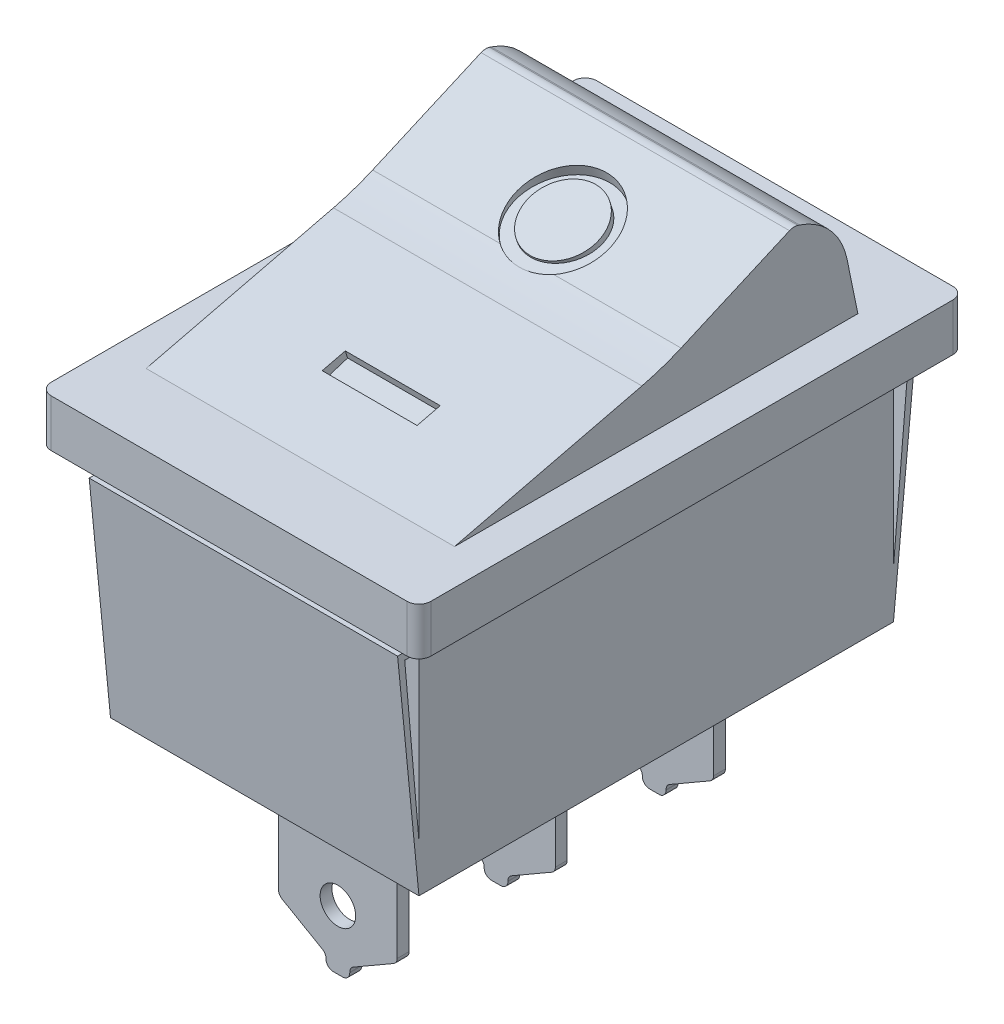
SolidWorks part; units mm, degrees
ref_plane "Alzado" through (0, 0, 0) normal (0, 0, 1) x (1, 0, 0)
ref_plane "Planta" through (0, 0, 0) normal (0, 1, 0) x (1, 0, 0)
ref_plane "Vista lateral" through (0, 0, 0) normal (1, 0, 0) x (0, 0, -1)
sketch "Croquis1" plane through (0, 0, 0) normal (0, 1, 0) x (1, 0, 0)
  line L1 (8, 11.5) -> (-8, 11.5)
  line L2 (8, 11.5) -> (8, -11.5)
  line L3 (8, -11.5) -> (-8, -11.5)
  line L4 (-8, 11.5) -> (-8, -11.5)
  line L5 (8, 11.5) -> (-8, -11.5) construction
  line L6 (8, -11.5) -> (-8, 11.5) construction
  point P0 (0, 0)
  dimension "D1" = 23
  dimension "D2" = 16
extrude "Saliente-Extruir1" add sketch "Croquis1" along normal blind 2
sketch "Croquis2" plane through (0, 0, 0) normal (0, -1, 0) x (1, 0, 0)
  line L1 (6.5, 10) -> (-6.5, 10)
  line L2 (6.5, 10) -> (6.5, -10)
  line L3 (6.5, -10) -> (-6.5, -10)
  line L4 (-6.5, 10) -> (-6.5, -10)
  line L5 (6.5, 10) -> (-6.5, -10) construction
  line L6 (6.5, -10) -> (-6.5, 10) construction
  point P0 (0, 0)
  dimension "D1" = 13
  dimension "D2" = 20
extrude "Saliente-Extruir2" add sketch "Croquis2" along normal blind 10
sketch "Croquis3" plane through (0, 0, 0) normal (1, 0, 0) x (0, 0, -1)
  line L1 (-11.5, 2) -> (11.5, 2) construction
  line L3 (8.5, 2) -> (-8.5, 2)
  line L4 (5.9762, 6.4869) -> (6.0484, 6.463)
  line L5 (8.0421, 4.2212) -> (8.5, 2)
  line L6 (5.7941, 6.5473) -> (8.5, 2) construction
  line L7 (-8.5, 2) -> (-0.6036, 3.9144)
  line L8 (1.0482, 4.4711) -> (5.6184, 6.4704)
  line L9 (-8.5, 2) -> (5.7941, 6.5473) construction
  arc A0 (-0.6036, 3.9144) -> (1.0482, 4.4711) centre (-2.9597, 13.6328) ccw
  arc A1 (8.0421, 4.2212) -> (6.0484, 6.463) centre (5.1039, 3.6155) ccw
  arc A2 (5.9762, 6.4869) -> (5.6184, 6.4704) centre (5.8188, 6.0124) ccw
  point P4 (0.2988, 4.1882)
  point P12 (0.2466, 4.1205)
  point P15 (7.6924, 5.9176)
  dimension "D9" = 10
  dimension "D10" = 3
  dimension "D11" = 0.5
  dimension "D1" = 3
  dimension "D2" = 3
  dimension "D3" = 15
  dimension "D4" = 120
  dimension "D5" = 2
  dimension "D6" = 4
  dimension "D7" = 170
  dimension "D8" = 9
extrude "Saliente-Extruir3" add sketch "Croquis3" along normal mid plane 13
ref_plane "Plano1" through (0, 4.265, 1.3514) normal (0, 0.9533, 0.302) x (1, 0, 0)
sketch "Croquis4" plane through (0, 4.265, 1.3514) normal (0, 0.9533, 0.302) x (1, 0, 0)
  line L0 (0, 4) -> (0, 0) construction
  line L1 (-2, -4.5) -> (-2, -3.5)
  line L2 (-2, -3.5) -> (2, -3.5)
  line L3 (2, -3.5) -> (2, -4.5)
  line L4 (2, -4.5) -> (-2, -4.5)
  line L5 (-2, -3.5) -> (2, -4.5) construction
  circle A0 centre (0, 4) radius 2
  circle A2 centre (0, 4) radius 1.5
  point P7 (0, -3.5)
  point P10 (0, -4)
  dimension "D1" = 4
  dimension "D3" = 3
  dimension "D2" = 4
  dimension "D4" = 1
  dimension "D5" = 4
  dimension "D6" = 4
extrude "Cortar-Extruir1" cut sketch "Croquis4" against normal blind 0.6
sketch "Croquis5" plane through (0, 0, 0) normal (1, 0, 0) x (0, 0, -1)
  line L0 (-10, 0) -> (-10, -0.2)
  line L1 (-10, -10) -> (-10, 0) construction
  line L2 (-10, -0.2) -> (-10.3, -0.2)
  line L3 (-10.3, -0.2) -> (-10.3, -0.5)
  line L4 (-10.3, -0.5) -> (-10.6, -0.5)
  line L5 (-10.6, -0.5) -> (-10.6, -0.8)
  line L6 (-10.6, -0.8) -> (-10.9, -0.8)
  line L7 (-10.9, -0.8) -> (-10, -10)
  line L9 (-10.6, -1.1) -> (-10.3, -1.1)
  line L10 (-10.3, -1.1) -> (-10.3, -0.8)
  line L11 (-10.3, -0.8) -> (-10, -0.8)
  line L12 (-10, -0.8) -> (-10, -0.2)
  line L13 (-10.6, -1.1) -> (-10, -8)
  line L14 (-11.5, 0) -> (11.5, 0) construction
  line L15 (-10, -8) -> (-10, -10)
  dimension "D1" = 0.3
  dimension "D2" = 0.3
  dimension "D3" = 0.3
  dimension "D4" = 0.3
  dimension "D5" = 0.2
  dimension "D6" = 0.3
  dimension "D7" = 0.3
  dimension "D8" = 0.3
  dimension "D9" = 0.6
  dimension "D10" = 2
extrude "Saliente-Extruir6" add sketch "Croquis5" along normal mid plane 13 contours L2 L3 L4 L5 L6 L7 L15 L13 L9 L10 L11 L12
mirror "Simetría2" about plane through (0, 0, 0) normal (0, 0, 1) of "Saliente-Extruir6"
fillet "Redondeo1" radius 0.5 4 edges at (8, 1, -11.5) (-8, 1, -11.5) (-8, 1, 11.5) (8, 1, 11.5)
sketch "Croquis6" plane through (0, 0, 0) normal (0, 0, 1) x (1, 0, 0)
  line L0 (2.5, -10) -> (-2.5, -10)
  line L1 (-6.5, -10) -> (6.5, -10) construction
  line L2 (-2.5, -10) -> (-2.5, -15.8268)
  line L3 (-2.35, -16.0866) -> (-0.65, -17.0681)
  line L4 (-0.5, -17.3279) -> (-0.5, -17.3547)
  line L5 (-0.2, -17.6547) -> (0.2, -17.6547)
  line L6 (0.5, -17.3547) -> (0.5, -17.3279)
  line L7 (0.65, -17.0681) -> (2.35, -16.0866)
  line L8 (2.5, -15.8268) -> (2.5, -10)
  line L9 (0, -10) -> (0, -15.1547) construction
  circle A0 centre (0, -15.1547) radius 0.75
  arc A1 (-2.5, -15.8268) -> (-2.35, -16.0866) centre (-2.2, -15.8268) ccw
  arc A2 (-0.65, -17.0681) -> (-0.5, -17.3279) centre (-0.8, -17.3279) cw
  arc A3 (-0.5, -17.3547) -> (-0.2, -17.6547) centre (-0.2, -17.3547) ccw
  arc A4 (0.2, -17.6547) -> (0.5, -17.3547) centre (0.2, -17.3547) ccw
  arc A5 (0.5, -17.3279) -> (0.65, -17.0681) centre (0.8, -17.3279) cw
  arc A6 (2.35, -16.0866) -> (2.5, -15.8268) centre (2.2, -15.8268) ccw
  point P4 (0, -10)
  point P21 (-0.5, -17.6547)
  point P24 (0.5, -17.6547)
  point P27 (0.5, -17.1547)
  point P30 (2.5, -16)
  dimension "D7" = 2.5
  dimension "D8" = 1.5
  dimension "D9" = 0.3
  dimension "D1" = 5
  dimension "D2" = 6
  dimension "D3" = 120
  dimension "D4" = 120
  dimension "D5" = 1
  dimension "D6" = 0.5
extrude "Saliente-Extruir7" add sketch "Croquis6" along normal mid plane 0.5
pattern_linear "MatrizL1" count 2 spacing 6.6667 along (0, 0, -1) of "Saliente-Extruir7"
pattern_linear "MatrizL2" count 2 spacing 6.6667 along (0, 0, 1) of "Saliente-Extruir7"
